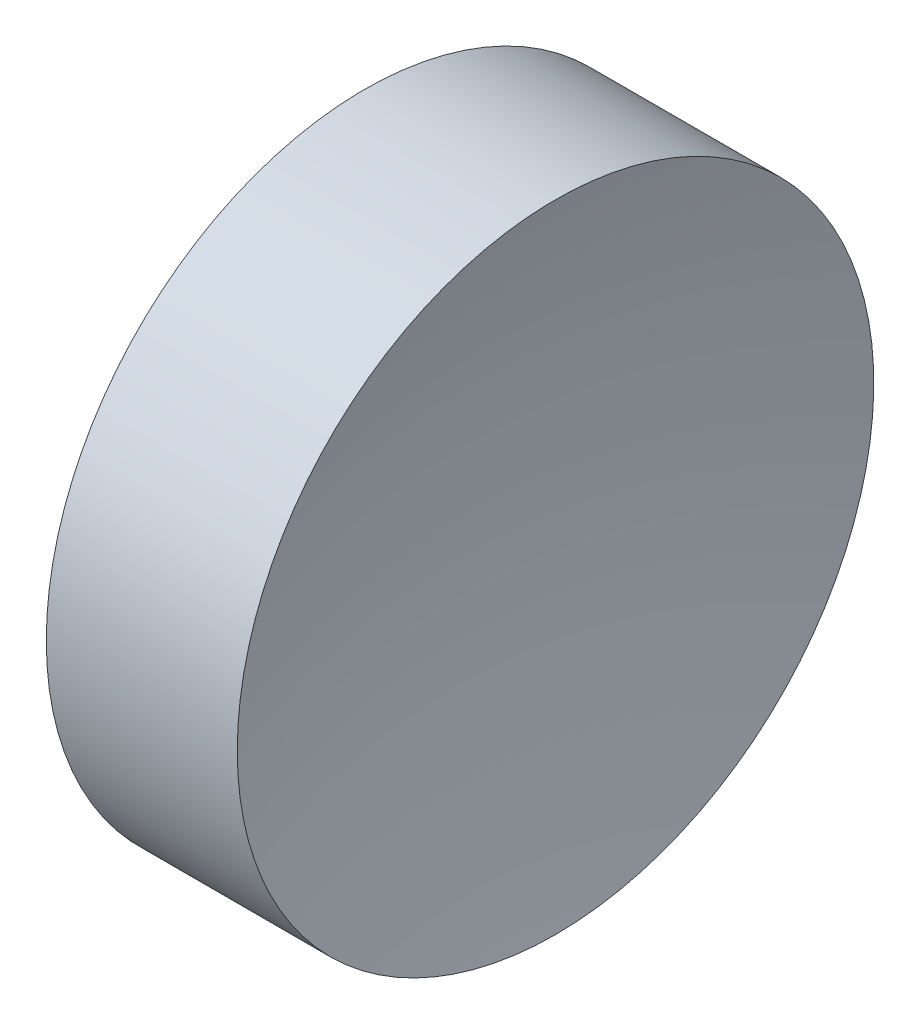
SolidWorks part; units mm, degrees
ref_plane "前视基准面" through (0, 0, 0) normal (0, 0, 1) x (1, 0, 0)
ref_plane "上视基准面" through (0, 0, 0) normal (0, 1, 0) x (1, 0, 0)
ref_plane "右视基准面" through (0, 0, 0) normal (1, 0, 0) x (0, 0, -1)
sketch "草图1" plane through (0, 0, 0) normal (0, 0, 1) x (1, 0, 0)
  line L0 (20.684, 13.0311) -> (26.997, 13.0311) construction
  line L1 (22.3093, 13.0311) -> (22.3093, 16.1811)
  line L2 (22.3093, 16.1811) -> (24.1995, 16.1811)
  line L3 (23.8093, 13.0311) -> (22.3093, 13.0311)
  arc A0 (24.1995, 16.1811) -> (23.8093, 13.0311) centre (36.7193, 13.0311) ccw
revolve "旋转1" add sketch "草图1" angle 360 about L0
